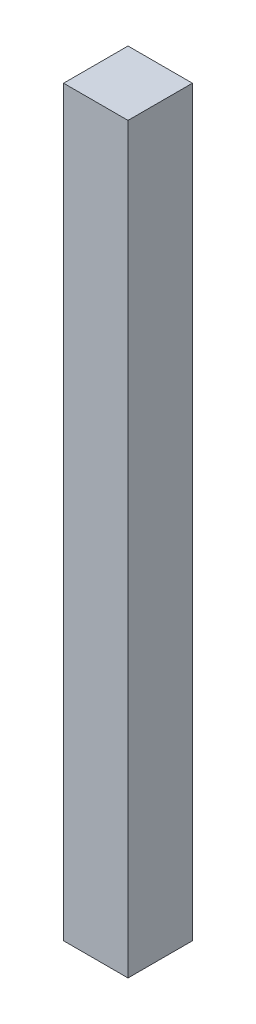
SolidWorks part; units mm, degrees
ref_plane "Front Plane" through (0, 0, 0) normal (0, 0, 1) x (1, 0, 0)
ref_plane "Top Plane" through (0, 0, 0) normal (0, 1, 0) x (1, 0, 0)
ref_plane "Right Plane" through (0, 0, 0) normal (1, 0, 0) x (0, 0, -1)
sketch "Sketch1" plane through (0, 0, 0) normal (0, 1, 0) x (1, 0, 0)
  line L1 (-12.7, -12.7) -> (12.7, -12.7)
  line L2 (-12.7, -12.7) -> (-12.7, 12.7)
  line L3 (-12.7, 12.7) -> (12.7, 12.7)
  line L4 (12.7, -12.7) -> (12.7, 12.7)
  line L5 (-12.7, -12.7) -> (12.7, 12.7) construction
  line L6 (-12.7, 12.7) -> (12.7, -12.7) construction
  point P0 (0, 0)
  dimension "D1" = 25.4
extrude "Boss-Extrude1" add sketch "Sketch1" along normal blind 292.85
